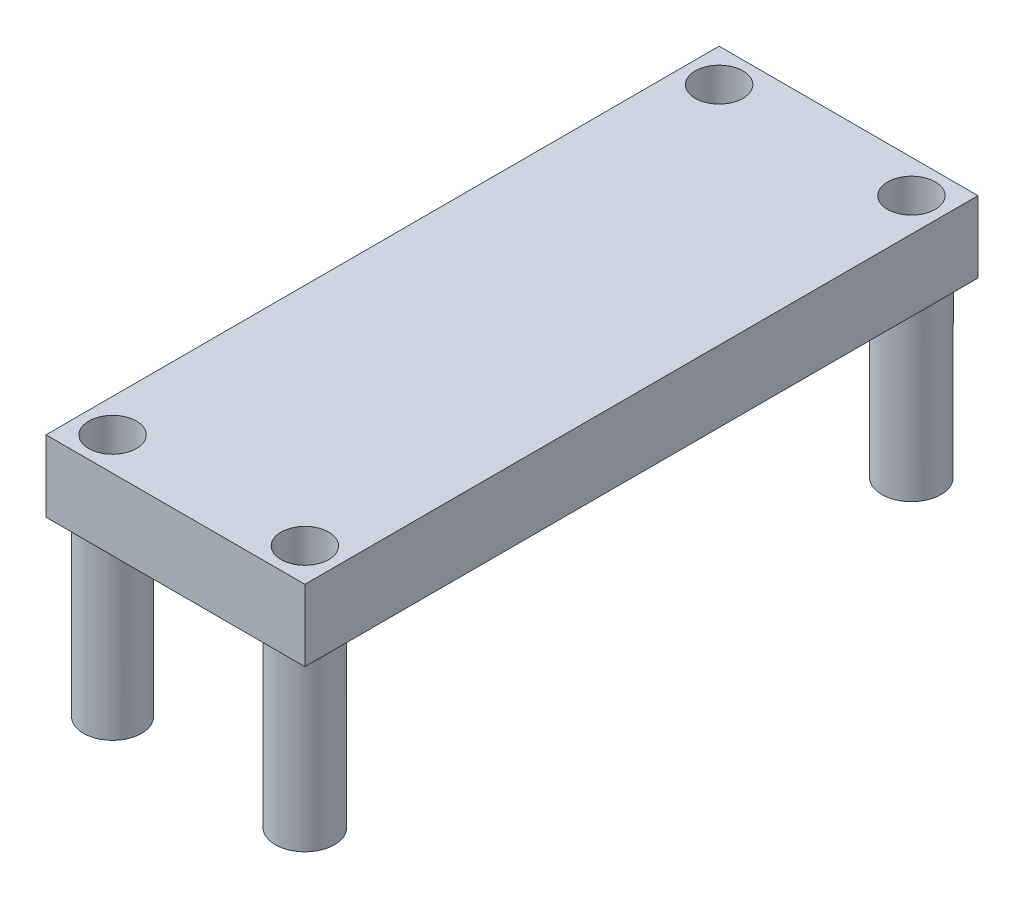
SolidWorks part; units mm, degrees
ref_plane "Front Plane" through (0, 0, 0) normal (0, 0, 1) x (1, 0, 0)
ref_plane "Top Plane" through (0, 0, 0) normal (0, 1, 0) x (1, 0, 0)
ref_plane "Right Plane" through (0, 0, 0) normal (1, 0, 0) x (0, 0, -1)
sketch "Sketch1" plane through (0, 0, 0) normal (0, 1, 0) x (1, 0, 0)
  line L1 (-16.8639, 11.4761) -> (0.9161, 11.4761)
  line L2 (-16.8639, 11.4761) -> (-16.8639, -34.7519)
  line L3 (-16.8639, -34.7519) -> (0.9161, -34.7519)
  line L4 (0.9161, 11.4761) -> (0.9161, -34.7519)
  dimension "D1" = 46.228
  dimension "D2" = 17.78
extrude "Boss-Extrude1" add sketch "Sketch1" along normal blind 4.9022
sketch "Sketch2" plane through (0, 0, 0) normal (0, -1, 0) x (1, 0, 0)
  line L0 (-16.8639, -11.4761) -> (-16.8639, 34.7519) construction
  line L1 (-16.8639, 34.7519) -> (0.9161, 34.7519) construction
  line L2 (0.9161, -11.4761) -> (-16.8639, -11.4761) construction
  line L3 (0.9161, 34.7519) -> (0.9161, -11.4761) construction
  circle A0 centre (-14.5779, 32.4659) radius 1.9939
  circle A1 centre (-1.3699, 32.4659) radius 2.032
  circle A2 centre (-1.3699, -9.1901) radius 2.032
  circle A3 centre (-14.5779, -9.1901) radius 2.032
  dimension "D1" = 3.9878
  dimension "D3" = 2.286
  dimension "D6" = 4.064
  dimension "D7" = 2.286
  dimension "D8" = 2.286
  dimension "D9" = 4.064
  dimension "D11" = 2.286
  dimension "D12" = 4.064
  dimension "D2" = 2.286
  dimension "D4" = 2.286
  dimension "D5" = 2.286
  dimension "D10" = 2.286
extrude "Boss-Extrude2" add sketch "Sketch2" along normal blind 11.8618
sketch "Sketch3" plane through (0, -11.8618, 0) normal (0, -1, 0) x (1, 0, 0)
  circle A0 centre (-14.5779, 32.4659) radius 1.6383
  circle A1 centre (-14.5779, -9.1901) radius 1.6383
  circle A2 centre (-1.3699, -9.1901) radius 1.6383
  circle A3 centre (-1.3699, 32.4659) radius 1.6383
  dimension "D1" = 3.2766
  dimension "D2" = 3.2766
  dimension "D3" = 3.2766
  dimension "D4" = 3.2766
extrude "Cut-Extrude1" cut sketch "Sketch3" against normal through all
